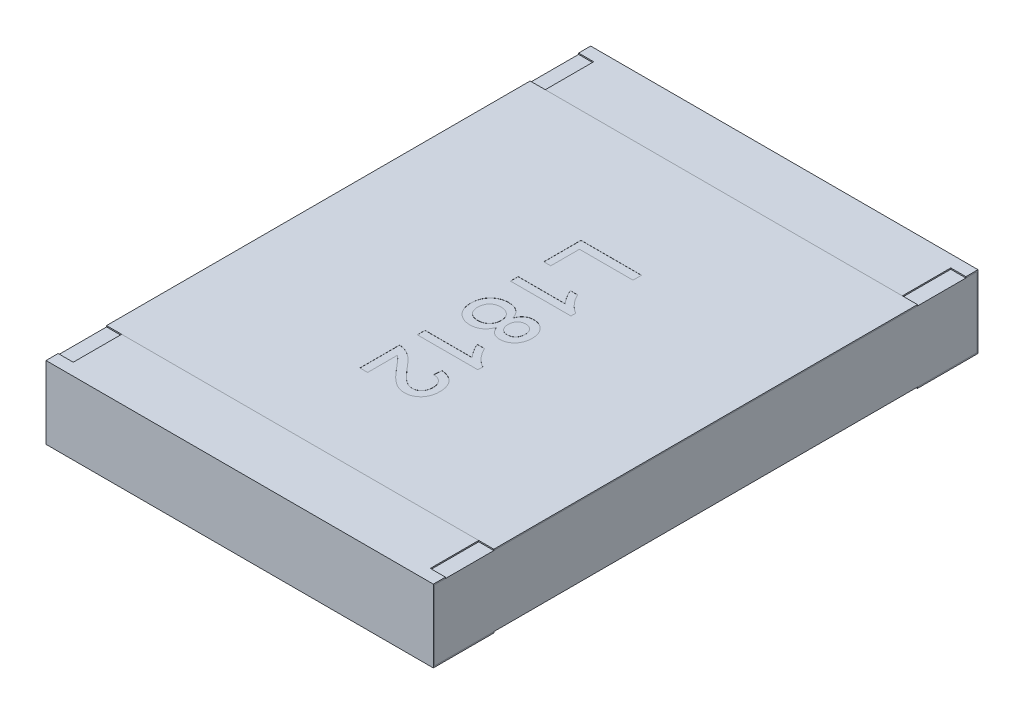
SolidWorks part; units mm, degrees
ref_plane "Front Plane" through (0, 0, 0) normal (0, 0, 1) x (1, 0, 0)
ref_plane "Top Plane" through (0, 0, 0) normal (0, 1, 0) x (1, 0, 0)
ref_plane "Right Plane" through (0, 0, 0) normal (1, 0, 0) x (0, 0, -1)
sketch "Sketch4" plane through (0, 0, 0) normal (1, 0, 0) x (0, 0, -1)
  line L0 (0, 0.1169) -> (0, -0.0721) construction
  line L1 (-2.25, 0) -> (0.3788, 0) construction
  line L2 (-2.25, 0.3) -> (-2.25, -0.3)
  line L3 (-2.25, -0.3) -> (-1.75, -0.3)
  line L4 (-1.75, 0.3) -> (-1.75, 0.29)
  line L5 (-1.75, 0.29) -> (-2.24, 0.29)
  line L6 (-2.24, 0.29) -> (-2.24, -0.29)
  line L7 (-2.24, -0.29) -> (-1.75, -0.29)
  line L8 (-1.75, -0.29) -> (-1.75, -0.3)
  line L9 (-1.75, 0.3) -> (-2.25, 0.3)
  line L10 (1.75, 0.3) -> (2.25, 0.3)
  line L11 (1.75, -0.29) -> (1.75, -0.3)
  line L12 (2.24, -0.29) -> (1.75, -0.29)
  line L13 (2.24, 0.29) -> (2.24, -0.29)
  line L14 (1.75, 0.29) -> (2.24, 0.29)
  line L15 (1.75, 0.3) -> (1.75, 0.29)
  line L16 (2.25, -0.3) -> (1.75, -0.3)
  line L17 (2.25, 0.3) -> (2.25, -0.3)
  dimension "LENGTH" = 2.25
  dimension "HEIGHT" = 0.6
  dimension "END CAP TOP LENGTH" = 0.5
  dimension "END CAP BOTTOM LENGTH" = 0.5
  dimension "D5" = 0.01
  dimension "D6" = 0.01
extrude "Boss-Extrude2" add sketch "Sketch4" along normal mid plane 3.2
sketch "Sketch5" plane through (0, 0, 0) normal (1, 0, 0) x (0, 0, -1)
  line L1 (-2.24, 0.29) -> (2.24, 0.29)
  line L2 (-2.24, 0.29) -> (-2.24, -0.29)
  line L3 (-2.24, -0.29) -> (2.24, -0.29)
  line L4 (2.24, 0.29) -> (2.24, -0.29)
extrude "Boss-Extrude3" add sketch "Sketch5" along normal up to surface and the other way up to surface separate body
sketch "Sketch6" plane through (0, 0.3, 0) normal (0, 1, 0) x (1, 0, 0)
  line L0 (-1.6, 2.25) -> (-1.6, 1.75) construction
  line L1 (-1.6, 2.15) -> (-1.475, 2.15)
  line L2 (-1.6, 2.15) -> (-1.6, 1.75)
  line L3 (-1.6, 1.75) -> (-1.475, 1.75)
  line L4 (-1.475, 2.15) -> (-1.475, 1.75)
  line L5 (1.6, 1.75) -> (-1.6, 1.75) construction
  line L6 (0, 0.0345) -> (0, -0.0345) construction
  line L7 (-0.0325, 0) -> (0.03, 0) construction
  line L8 (1.6, 2.15) -> (1.6, 1.75)
  line L9 (1.6, 1.75) -> (1.475, 1.75)
  line L10 (1.475, 2.15) -> (1.475, 1.75)
  line L11 (1.6, 2.15) -> (1.475, 2.15)
  line L12 (1.6, -2.15) -> (1.475, -2.15)
  line L13 (1.6, -2.15) -> (1.6, -1.75)
  line L14 (1.6, -1.75) -> (1.475, -1.75)
  line L15 (1.475, -2.15) -> (1.475, -1.75)
  line L16 (-1.6, -2.15) -> (-1.475, -2.15)
  line L17 (-1.6, -2.15) -> (-1.6, -1.75)
  line L18 (-1.6, -1.75) -> (-1.475, -1.75)
  line L19 (-1.475, -2.15) -> (-1.475, -1.75)
  dimension "TOP CUT WIDTH" = 0.125
  dimension "TOP CUT LENGTH" = 0.4
extrude "Cut-Extrude1" cut sketch "Sketch6" against normal up to surface (0.01 mm away) up to face at (0, 0.29, 0)
sketch "Sketch7" plane through (0, 0.29, 0) normal (0, 1, 0) x (1, 0, 0)
  line L1 (-1.6, 1.75) -> (1.6, 1.75)
  line L2 (-1.6, 1.75) -> (-1.6, -1.75)
  line L3 (-1.6, -1.75) -> (1.6, -1.75)
  line L4 (1.6, 1.75) -> (1.6, -1.75)
  line L5 (1.475, -1.75) -> (-1.475, -1.75) construction
  line L6 (1.475, 1.75) -> (-1.475, 1.75) construction
  line L7 (-1.6, -2.24) -> (-1.6, 2.24) construction
  line L8 (1.6, 2.24) -> (1.6, -2.24) construction
extrude "Boss-Extrude4" add sketch "Sketch7" along normal up to surface (0.01 mm away) separate body up to face at (0, 0.3, -2.075)
sketch "Sketch14" plane through (0, 0.3, 0) normal (0, 1, 0) x (1, 0, 0)
  line L0 (-0.25, 0.8778) -> (-0.25, -0.8778) construction
  line L1 (0, 0) -> (-0.25, 0) construction
  text T0 "L1812" font "Arial" height 0.5
  dimension "D1" = 0.25
extrude "TEXT1812" cut sketch "Sketch14" against normal blind 0.001
